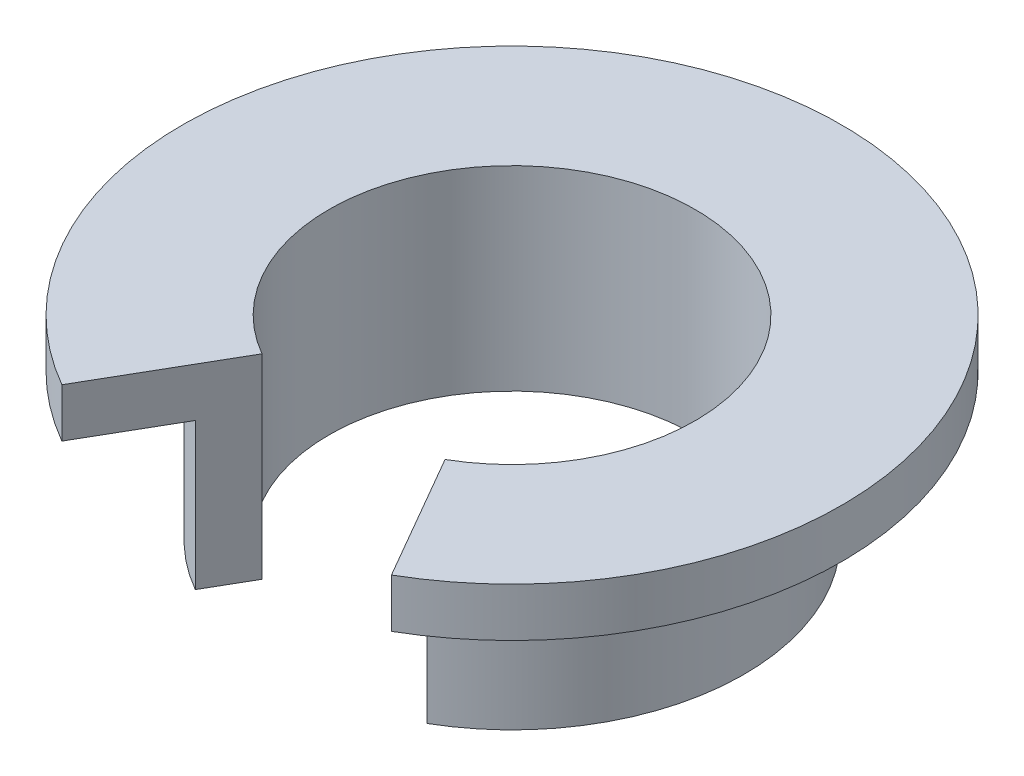
SolidWorks part; units mm, degrees
ref_plane "Front Plane" through (0, 0, 0) normal (0, 0, 1) x (1, 0, 0)
ref_plane "Top Plane" through (0, 0, 0) normal (0, 1, 0) x (1, 0, 0)
ref_plane "Right Plane" through (0, 0, 0) normal (1, 0, 0) x (0, 0, -1)
sketch "Sketch1" plane through (0, 0, 0) normal (0, 0, 1) x (1, 0, 0)
  line L0 (0, 0) -> (0, 12.4335) construction
  line L1 (7.5, 0) -> (7.5, 8)
  line L2 (7.5, 8) -> (13.5, 8)
  line L3 (13.5, 8) -> (13.5, 6)
  line L4 (13.5, 6) -> (9.5, 6)
  line L5 (9.5, 6) -> (9.5, 0)
  line L6 (9.5, 0) -> (7.5, 0)
  dimension "D1" = 15
  dimension "D2" = 19
  dimension "D3" = 27
  dimension "D4" = 8
  dimension "D5" = 6
revolve "Revolve1" add sketch "Sketch1" angle 360 about L0
sketch "Sketch2" plane through (0, 0, 0) normal (0, 1, 0) x (1, 0, 0)
  line L0 (0, 0) -> (0, -18.6945) construction
  line L1 (-9.0912, -15.7464) -> (0, 0)
  line L2 (0, 0) -> (8.6255, -14.9399)
  line L3 (-9.0912, -15.7464) -> (8.6255, -14.9399)
  dimension "D1" = 30
  dimension "D2" = 30
extrude "Cut-Extrude1" cut sketch "Sketch2" along normal blind 10
